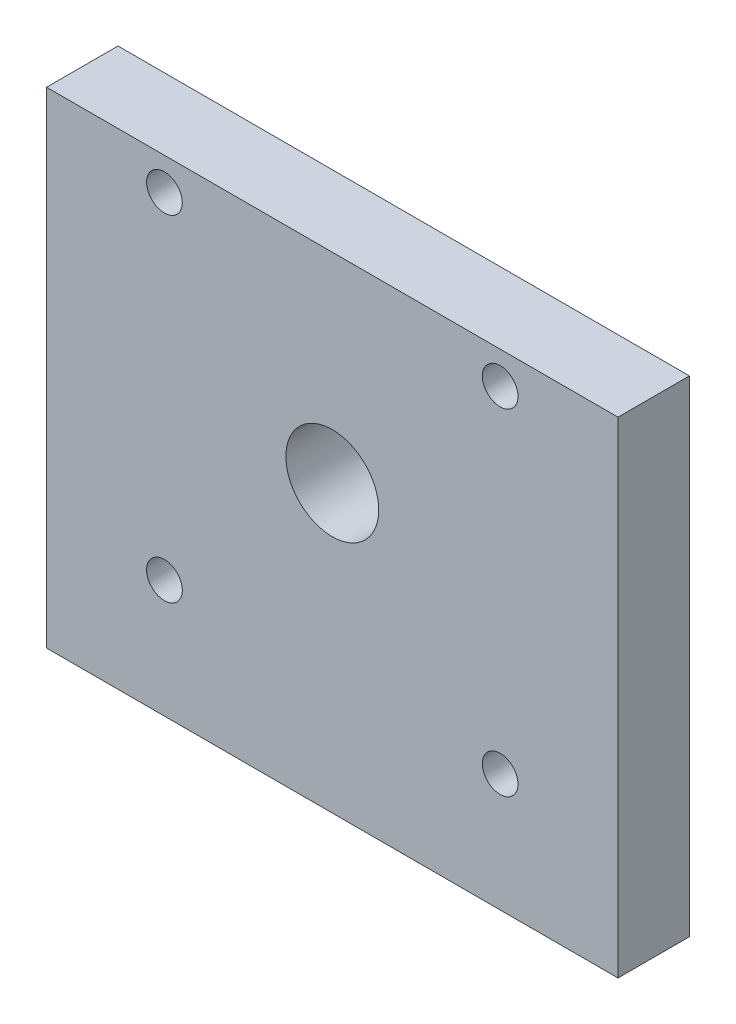
SolidWorks part; units mm, degrees
ref_plane "前视基准面" through (0, 0, 0) normal (0, 0, 1) x (1, 0, 0)
ref_plane "上视基准面" through (0, 0, 0) normal (0, 1, 0) x (1, 0, 0)
ref_plane "右视基准面" through (0, 0, 0) normal (1, 0, 0) x (0, 0, -1)
sketch "草图1" plane through (0, 0, 0) normal (0, 0, 1) x (1, 0, 0)
  line L0 (3.948, 82.6026) -> (3.948, -79.6916) construction
  line L1 (-36.052, 24.9315) -> (43.948, 24.9315)
  line L2 (-36.052, 24.9315) -> (-36.052, -43.0685)
  line L3 (-36.052, -43.0685) -> (43.948, -43.0685)
  line L4 (43.948, 24.9315) -> (43.948, -43.0685)
  line L5 (-59.3284, -9.0685) -> (78.491, -9.0685) construction
  line L6 (-37.8239, -3.0685) -> (58.2141, -3.0685) construction
  circle A0 centre (3.948, -3.0685) radius 6.5
  circle A1 centre (-19.552, 20.4315) radius 2.5
  circle A2 centre (27.448, 20.4315) radius 2.5
  circle A3 centre (27.448, -26.5685) radius 2.5
  circle A4 centre (-19.552, -26.5685) radius 2.5
  dimension "D3" = 13
  dimension "D4" = 40
  dimension "D5" = 23.5
  dimension "D7" = 5
  dimension "D1" = 80
  dimension "D2" = 68
  dimension "D6" = 23.5
extrude "凸台-拉伸1" add sketch "草图1" along normal blind 10
